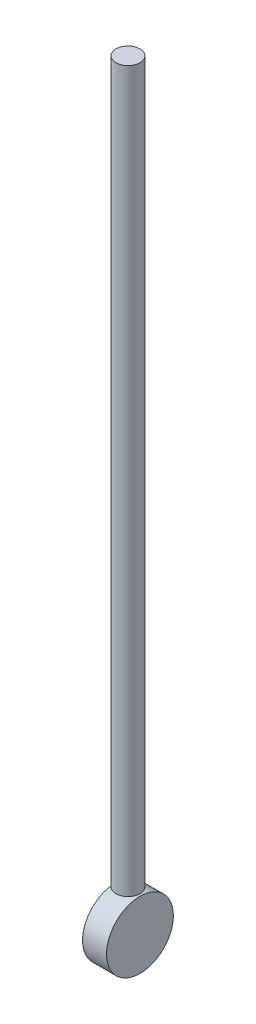
SolidWorks part; units mm, degrees
ref_plane "Front Plane" through (0, 0, 0) normal (0, 0, 1) x (1, 0, 0)
ref_plane "Top Plane" through (0, 0, 0) normal (0, 1, 0) x (1, 0, 0)
ref_plane "Right Plane" through (0, 0, 0) normal (1, 0, 0) x (0, 0, -1)
sketch "Sketch1" plane through (0, 0, 0) normal (0, 1, 0) x (1, 0, 0)
  circle A0 centre (0, 0) radius 6.35
  dimension "D1" = 12.7
extrude "Boss-Extrude1" add sketch "Sketch1" along normal blind 381
sketch "Sketch2" plane through (0, 0, 0) normal (1, 0, 0) x (0, 0, -1)
  circle A0 centre (0, -18.8638) radius 17.7006
extrude "Boss-Extrude2" add sketch "Sketch2" along normal mid plane 12.7 separate body
